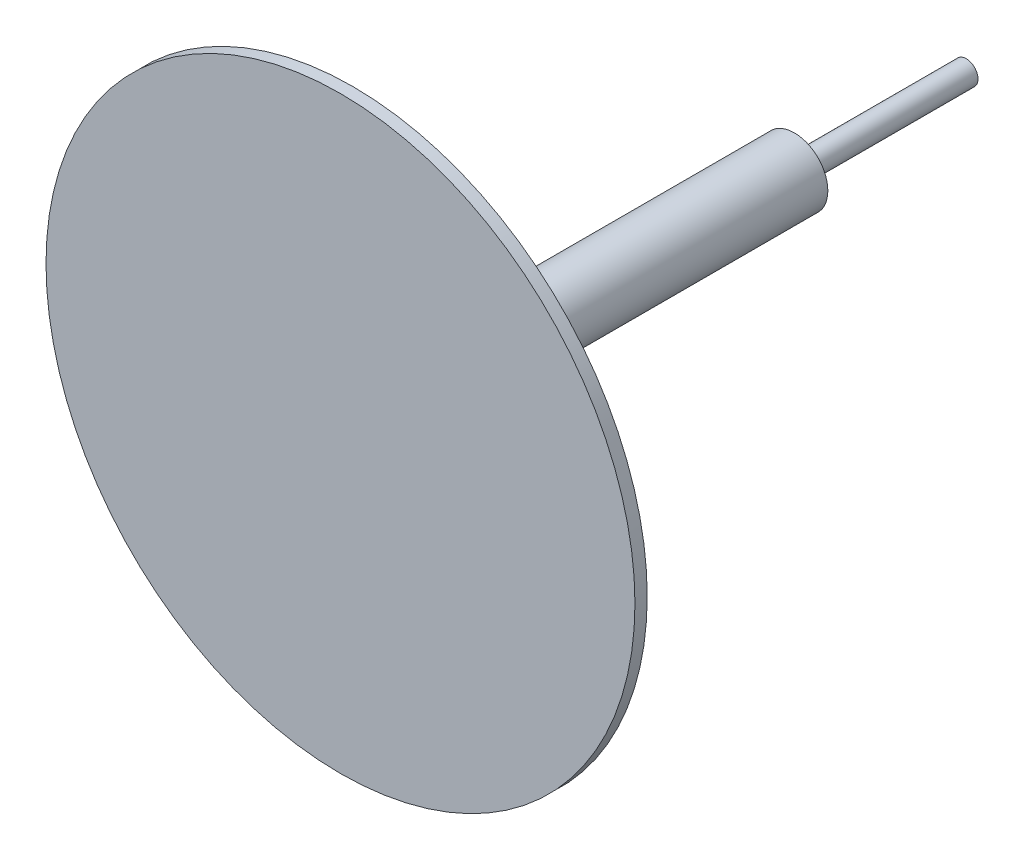
SolidWorks part; units mm, degrees
ref_plane "Front Plane" through (0, 0, 0) normal (0, 0, 1) x (1, 0, 0)
ref_plane "Top Plane" through (0, 0, 0) normal (0, 1, 0) x (1, 0, 0)
ref_plane "Right Plane" through (0, 0, 0) normal (1, 0, 0) x (0, 0, -1)
sketch "Sketch1" plane through (0, 0, 0) normal (0, 0, 1) x (1, 0, 0)
  circle A0 centre (0, 0) radius 15.24
  dimension "D1" = 30.48
extrude "Boss-Extrude1" add sketch "Sketch1" along normal blind 0.635
sketch "Sketch2" plane through (0, 0, 0) normal (0, 0, -1) x (-1, 0, 0)
  circle A0 centre (0, 0) radius 1.7272
  dimension "D1" = 3.4544
extrude "Boss-Extrude2" add sketch "Sketch2" along normal blind 22.86
sketch "Sketch3" plane through (0, 0, -22.86) normal (0, 0, -1) x (-1, 0, 0)
  circle A0 centre (0, 0) radius 0.6096
  dimension "D1" = 1.2192
extrude "Boss-Extrude3" add sketch "Sketch3" along normal blind 8.89
